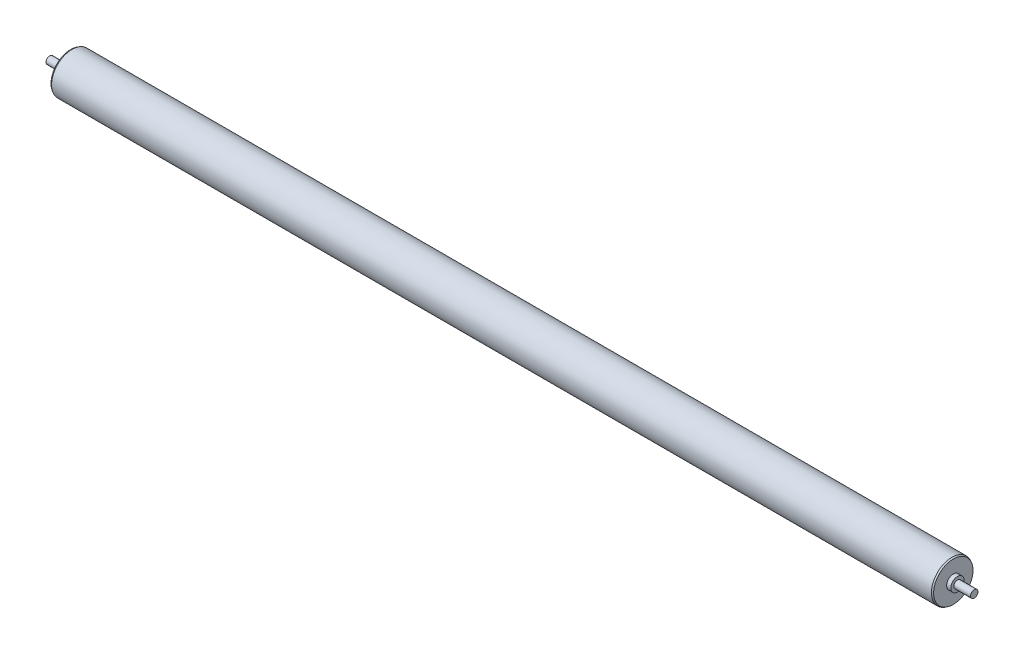
SolidWorks part; units mm, degrees
material "Galvanized Steel"
ref_plane "Front Plane" through (0, 0, 0) normal (0, 0, 1) x (1, 0, 0)
ref_plane "Top Plane" through (0, 0, 0) normal (0, 1, 0) x (1, 0, 0)
ref_plane "Right Plane" through (0, 0, 0) normal (1, 0, 0) x (0, 0, -1)
sketch "Sketch1" plane through (0, 0, 0) normal (0, 0, 1) x (1, 0, 0)
  line L0 (-381, 0) -> (381, 0) construction
  line L1 (-381, 0) -> (-393.7, 0) construction
  line L2 (381, 0) -> (393.7, 0) construction
  line L3 (-393.7, 3.175) -> (-393.7, -3.175) construction
  line L4 (-381, -3.175) -> (-381, 3.175) construction
  line L5 (381, -3.175) -> (381, 3.175) construction
  point P4 (-379.4125, 0)
  point P6 (379.4125, 0)
  point P7 (-374.65, 0)
  point P8 (374.65, 0)
  dimension "BF" = 762
  dimension "D1" = 787.4
  dimension "D2" = 1.5875
  dimension "D3" = 1.5875
  dimension "D4" = 4.7625
  dimension "D5" = 4.7625
  dimension "Axle Dia" = 6.35
sketch "Sketch2" plane through (0, 0, 0) normal (0, 0, 1) x (1, 0, 0)
  line L0 (-393.7, 0) -> (-393.7, 3.175)
  line L1 (-393.7, 3.175) -> (-379.4125, 3.175)
  line L2 (-379.4125, 3.175) -> (-379.4125, 5.715)
  line L3 (-379.4125, 5.715) -> (-375.8406, 5.715)
  line L4 (-375.8406, 5.715) -> (-375.8406, 16.7751)
  line L5 (-375.8406, 16.7751) -> (-374.65, 17.4625)
  line L6 (-374.65, 17.4625) -> (374.65, 17.4625)
  line L7 (0, 0) -> (0, 17.4625) construction
  line L8 (-381, 0) -> (-393.7, 0) construction
  line L9 (-393.7, 0) -> (0, 0) construction
  line L10 (-381, 0) -> (381, 0) construction
  line L11 (375.8406, 16.7751) -> (374.65, 17.4625)
  line L12 (375.8406, 5.715) -> (375.8406, 16.7751)
  line L13 (379.4125, 5.715) -> (375.8406, 5.715)
  line L14 (379.4125, 3.175) -> (379.4125, 5.715)
  line L15 (393.7, 3.175) -> (379.4125, 3.175)
  line L16 (393.7, 0) -> (393.7, 3.175)
  line L17 (-393.7, 0) -> (393.7, 0)
  dimension "D4" = 4.7625
  dimension "D1" = 30
  dimension "D2" = 11.43
  dimension "D3" = 34.925
  dimension "D5" = 3.5719
revolve "Revolve1" add sketch "Sketch2" angle 360 mid plane about L17
equation "\"D1@Sketch1\" = \"BF@Sketch1\"+1"
equation "\"D2@Sketch2\" = \"Axle Dia@Sketch1\"*1.8"
equation "\"D5@Sketch2\" = \"D4@Sketch2\"*.75"
